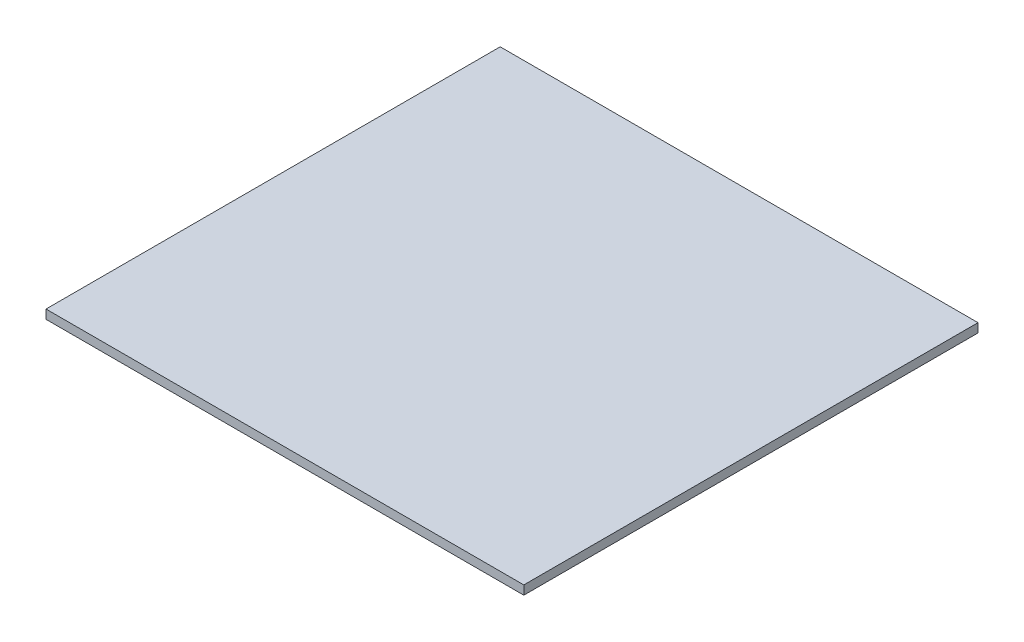
SolidWorks part; units mm, degrees
material "FR-4"
ref_plane "Front Plane" through (0, 0, 0) normal (0, 0, 1) x (1, 0, 0)
ref_plane "Top Plane" through (0, 0, 0) normal (0, 1, 0) x (1, 0, 0)
ref_plane "Right Plane" through (0, 0, 0) normal (1, 0, 0) x (0, 0, -1)
sketch "Sketch2" plane through (0, 0, 0) normal (0, 1, 0) x (1, 0, 0)
  line L4 (0, 0) -> (0, 86.5)
  line L5 (0, 86.5) -> (91, 86.5)
  line L6 (91, 86.5) -> (91, 0)
  line L7 (91, 0) -> (0, 0)
  line L8 (0, 86.5) -> (6, 86.5) construction
  line L9 (6, 86.5) -> (6, 0) construction
  line L10 (91, 86.5) -> (85, 86.5) construction
  line L11 (85, 86.5) -> (85, 0) construction
  dimension "D1" = 86.5
  dimension "D2" = 91
  dimension "D3" = 79
  dimension "D4" = 6
extrude "PCB" add sketch "Sketch2" along normal blind 1.7
